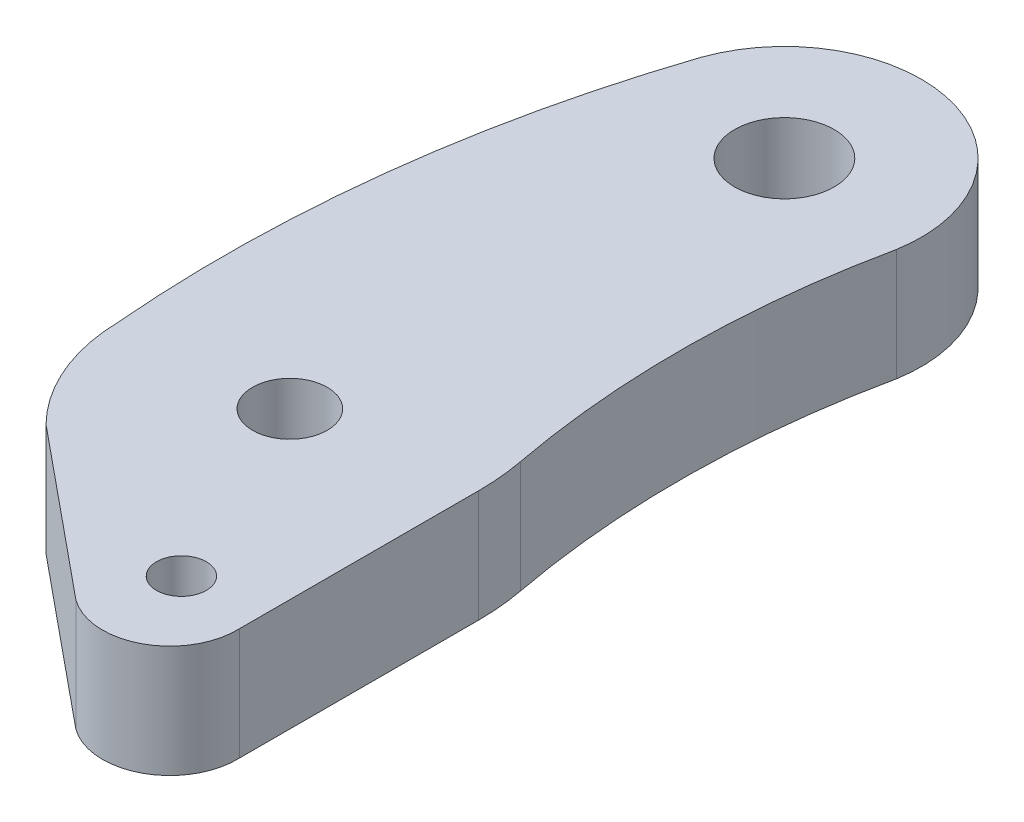
SolidWorks part; units mm, degrees
ref_plane "Front Plane" through (0, 0, 0) normal (0, 0, 1) x (1, 0, 0)
ref_plane "Top Plane" through (0, 0, 0) normal (0, 1, 0) x (1, 0, 0)
ref_plane "Right Plane" through (0, 0, 0) normal (1, 0, 0) x (0, 0, -1)
sketch "Sketch1" plane through (0, 0, 0) normal (0, 1, 0) x (1, 0, 0)
  line L0 (-17.2903, -3.2143) -> (19.9736, -3.2143) construction
  line L1 (-4.3573, -5.4354) -> (2.3443, -10.9381)
  line L2 (6.6409, 1.9306) -> (6.635, -8.6594)
  circle A0 centre (0, 0) radius 1.5
  circle A1 centre (3.6402, -7.9954) radius 1
  circle A2 centre (1.2162, 18.6426) radius 2
  arc A3 (6.5586, 17.3357) -> (-4.0433, 20.2514) centre (1.2162, 18.6426) ccw
  arc A4 (-3.9672, 20.4819) -> (-6.4565, -0.4684) centre (45.6838, 3.9594) ccw
  arc A5 (-6.4565, -0.4684) -> (-4.3573, -5.4354) centre (0.8616, -0.3027) ccw
  arc A6 (6.6379, 17.718) -> (6.6409, 1.9306) centre (43.7197, 9.8315) ccw
  arc A7 (2.3443, -10.9381) -> (6.635, -8.6594) centre (3.9364, -8.7571) ccw
  point P9 (1.2162, 24.1426)
  point P23 (3.9364, -11.4574)
  point P24 (0, 0)
  dimension "D2" = 4
  dimension "D3" = 3
  dimension "D5" = 2
  dimension "D1" = 35.6
  dimension "D4" = 5.5
extrude "Boss-Extrude1" add sketch "Sketch1" along normal blind 4.5 contours A5 L0 L2 A6 A3 A4 A2 A0 | L0 A5 L1 A7 L2 A1
fillet "Fillet1" radius 10 1 edges at (6.6409, 2.25, -1.9306)
